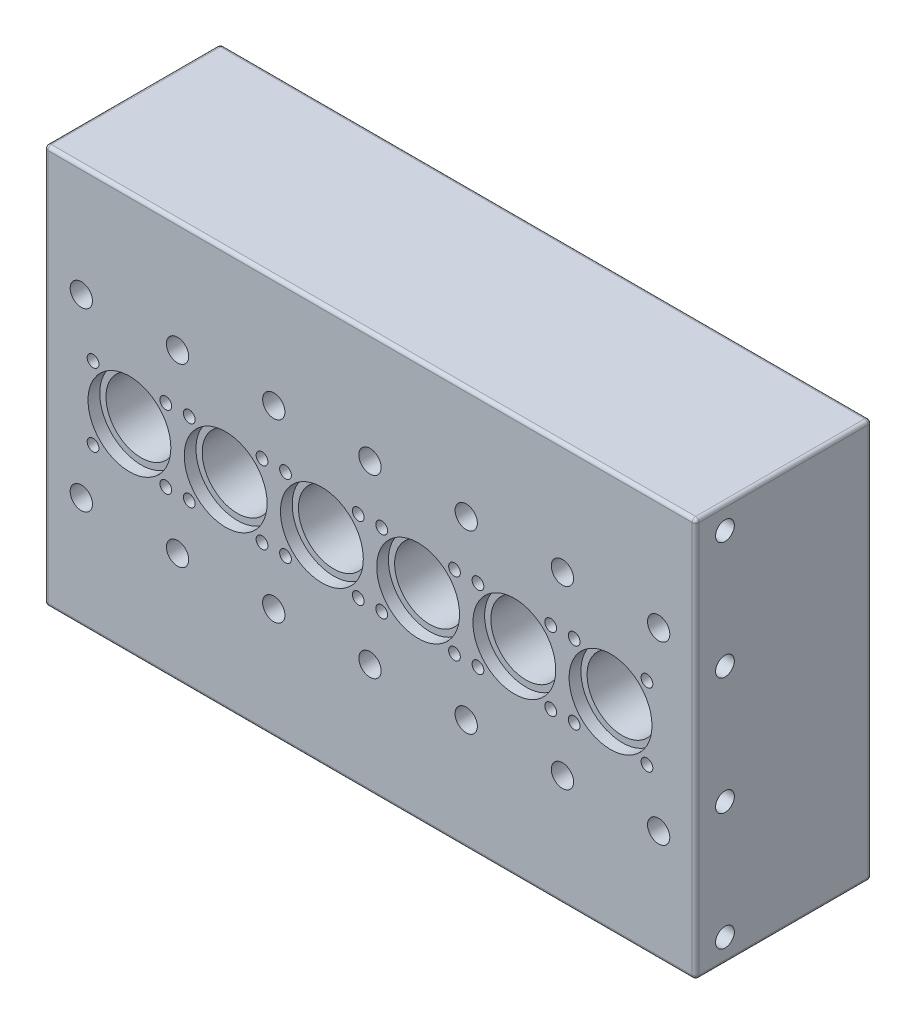
SolidWorks part; units mm, degrees
ref_plane "Front Plane" through (0, 0, 0) normal (0, 0, 1) x (1, 0, 0)
ref_plane "Top Plane" through (0, 0, 0) normal (0, 1, 0) x (1, 0, 0)
ref_plane "Right Plane" through (0, 0, 0) normal (1, 0, 0) x (0, 0, -1)
sketch "Sketch1" plane through (0, 0, 0) normal (0, 0, 1) x (1, 0, 0)
  line L1 (0, 0) -> (555, 0)
  line L2 (0, 0) -> (0, 340)
  line L3 (0, 340) -> (555, 340)
  line L4 (555, 0) -> (555, 340)
  dimension "D1" = 340
  dimension "D2" = 555
extrude "Boss-Extrude1" add sketch "Sketch1" along normal mid plane 150
sketch "Sketch3" plane through (0, 0, 75) normal (0, 0, 1) x (1, 0, 0)
  line L0 (0, 340) -> (0, 0) construction
  circle A0 centre (72.5, 170) radius 35.3
  dimension "D1" = 70.6
  dimension "D2" = 72.5
  dimension "D3" = 170
extrude "Cut-Extrude1" cut sketch "Sketch3" against normal blind 10
sketch "Sketch5" plane through (0, 0, 65) normal (0, 0, 1) x (1, 0, 0)
  circle A0 centre (72.5, 170) radius 30
  dimension "D1" = 60
extrude "Cut-Extrude2" cut sketch "Sketch5" against normal blind 110
sketch "Sketch6" plane through (0, 0, -45) normal (0, 0, 1) x (1, 0, 0)
  circle A0 centre (72.5, 170) radius 27
  dimension "D1" = 54
extrude "Cut-Extrude3" cut sketch "Sketch6" against normal blind 218
sketch "Sketch7" plane through (0, 0, -75) normal (0, 0, -1) x (-1, 0, 0)
  line L1 (-88.5, 204) -> (-56.5, 204)
  line L2 (-88.5, 204) -> (-88.5, 136)
  line L3 (-88.5, 136) -> (-56.5, 136)
  line L4 (-56.5, 204) -> (-56.5, 136)
  circle A0 centre (-72.5, 170) radius 27 construction
  dimension "D1" = 68
  dimension "D2" = 32
  dimension "D3" = 16
  dimension "D4" = 34
extrude "Cut-Extrude4" cut sketch "Sketch7" against normal blind 30
sketch "Sketch8" plane through (0, 0, 75) normal (0, 0, 1) x (1, 0, 0)
  circle A0 centre (41.5, 201) radius 5
  circle A1 centre (72.5, 170) radius 35.3 construction
  dimension "D1" = 10
  dimension "D2" = 31
  dimension "D3" = 31
extrude "Cut-Extrude5" cut sketch "Sketch8" against normal blind 23
pattern_linear "LPattern1" count 2 spacing 62 along (1, 0, 0) count 2 spacing 62 along (0, -1, 0) of "Cut-Extrude5"
pattern_linear "LPattern2" count 6 spacing 82 along (1, 0, 0) of "Cut-Extrude1", "Cut-Extrude2", "Cut-Extrude3", "Cut-Extrude4", "Cut-Extrude5", "LPattern1"
sketch "Sketch9" plane through (0, 0, 75) normal (0, 0, 1) x (1, 0, 0)
  circle A0 centre (31.5, 245) radius 9.5
  circle A6 centre (72.5, 170) radius 35.3 construction
  dimension "D1" = 19
  dimension "D2" = 41
  dimension "D3" = 75
extrude "Cut-Extrude6" cut sketch "Sketch9" against normal through all
pattern_linear "LPattern3" count 7 spacing 82 along (1, 0, 0) count 2 spacing 150 along (0, -1, 0) of "Cut-Extrude6"
sketch "Sketch14" plane through (555, 0, 0) normal (1, 0, 0) x (0, 0, -1)
  circle A0 centre (-50, 20) radius 8
  dimension "D1" = 20
  dimension "D2" = 25
extrude "Cut-Extrude7" cut sketch "Sketch14" against normal through all
pattern_linear "LPattern4" count 4 spacing 100 along (0, 1, 0) of "Cut-Extrude7"
fillet "Fillet1" radius 3 12 edges at (0, 170, -75) (277.5, 0, -75) (0, 0, 0) (0, 340, 0) (0, 170, 75) (277.5, 340, -75) (277.5, 340, 75) (277.5, 0, 75) (555, 170, 75) (555, 0, 0) (555, 170, -75) (555, 340, 0)
